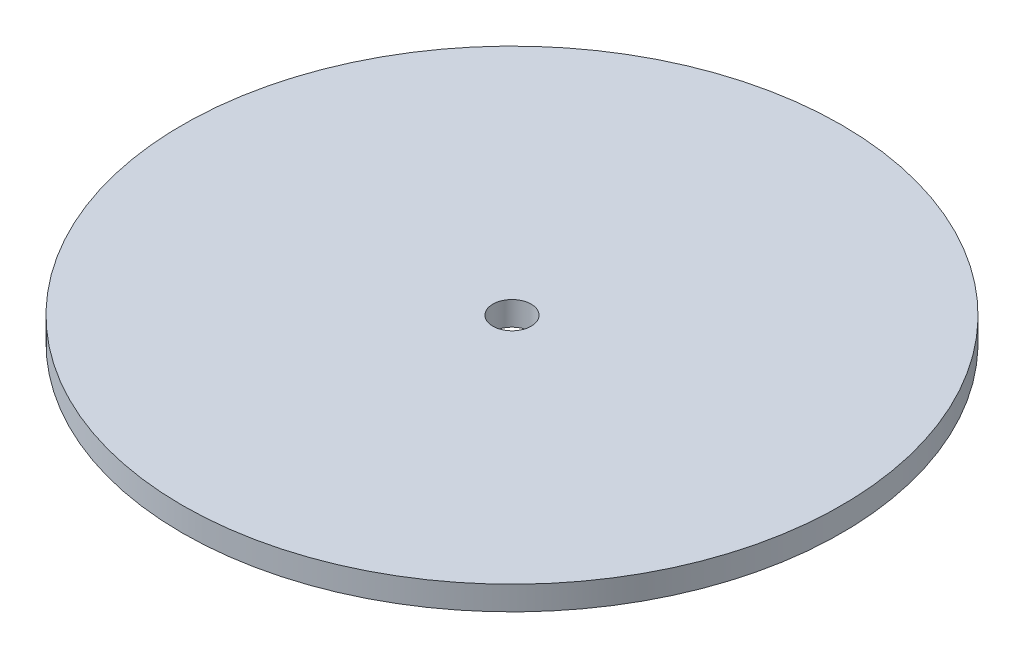
SolidWorks part; units mm, degrees
ref_plane "Front Plane" through (0, 0, 0) normal (0, 0, 1) x (1, 0, 0)
ref_plane "Top Plane" through (0, 0, 0) normal (0, 1, 0) x (1, 0, 0)
ref_plane "Right Plane" through (0, 0, 0) normal (1, 0, 0) x (0, 0, -1)
sketch "Sketch2" plane through (0, 0, 0) normal (0, 1, 0) x (1, 0, 0)
  circle A0 centre (0, 0) radius 137.5
  dimension "D1" = 275
extrude "Boss-Extrude1" add sketch "Sketch2" along normal blind 10
sketch "Sketch4" plane through (0, 10, 0) normal (0, 1, 0) x (1, 0, 0)
  circle A0 centre (0, 0) radius 8
  dimension "D1" = 16
extrude "Cut-Extrude1" cut sketch "Sketch4" against normal through all
